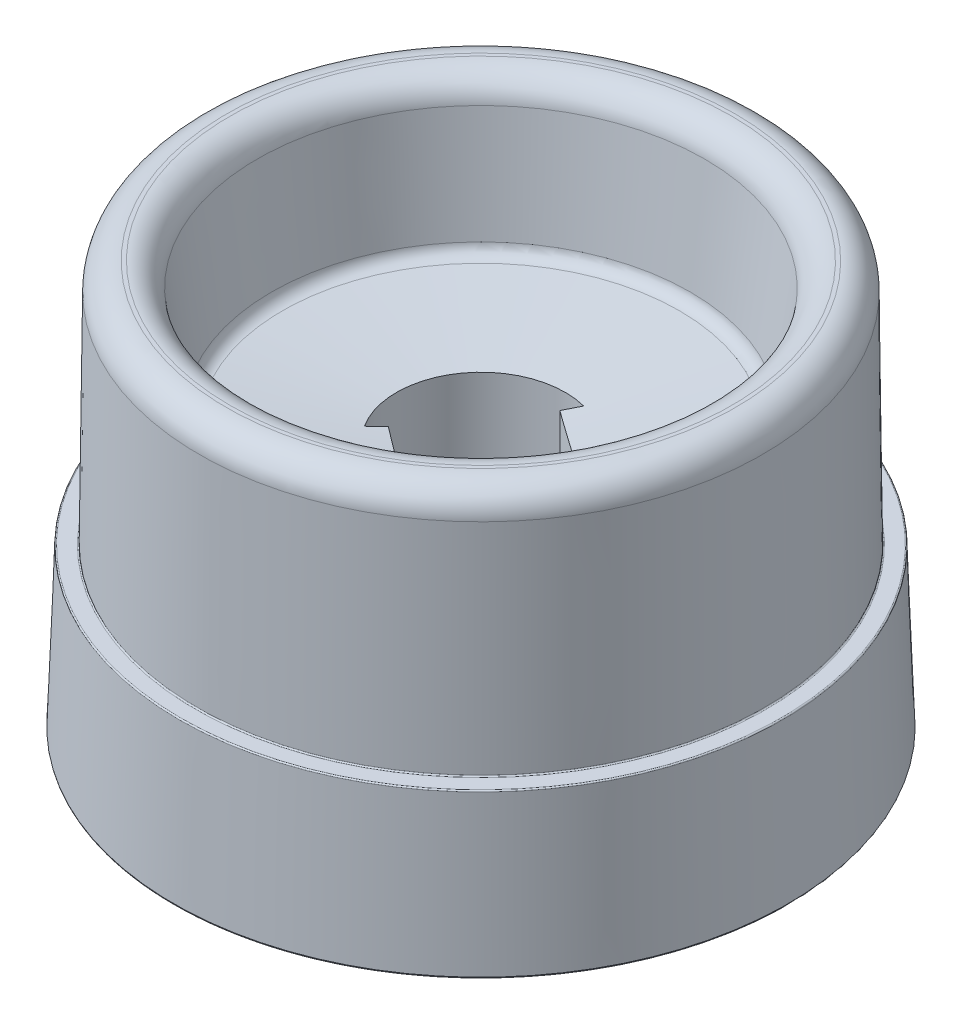
SolidWorks part; units mm, degrees
material "Nikiel"
ref_plane "Płaszczyzna przednia" through (0, 0, 0) normal (0, 0, 1) x (1, 0, 0)
ref_plane "Płaszczyzna górna" through (0, 0, 0) normal (0, 1, 0) x (1, 0, 0)
ref_plane "Płaszczyzna prawa" through (0, 0, 0) normal (1, 0, 0) x (0, 0, -1)
sketch "Szkic1" plane through (0, 0, 0) normal (0, 0, 1) x (1, 0, 0)
  line L0 (9.7791, 0) -> (12.2282, 0)
  line L1 (11.4094, 6.35) -> (12.0018, 6.35)
  line L2 (0, 4.2) -> (9.1594, 4.2)
  line L3 (0, 4.2) -> (0, 9.53)
  line L4 (12.2781, 0.0518) -> (12.0517, 6.3018)
  line L5 (11.3594, 6.3994) -> (11.2621, 15.1022)
  line L6 (10.1721, 16.18) -> (10.025, 16.18)
  line L8 (9.7291, 0.049) -> (9.6593, 3.7095)
  line L9 (8.9445, 15.2333) -> (8.3718, 10.9144)
  line L10 (7.9358, 10.4837) -> (0, 9.53)
  arc A1 (11.2621, 15.1022) -> (10.1721, 16.18) centre (10.1721, 15.09) ccw
  arc A2 (8.9445, 15.2333) -> (10.025, 16.18) centre (10.025, 15.09) cw
  arc A3 (11.3594, 6.3994) -> (11.4094, 6.35) centre (11.4094, 6.4) ccw
  arc A4 (12.0018, 6.35) -> (12.0517, 6.3018) centre (12.0018, 6.3) cw
  arc A5 (9.1594, 4.2) -> (9.6593, 3.7095) centre (9.1594, 3.7) cw
  arc A6 (9.7291, 0.049) -> (9.7791, 0) centre (9.7791, 0.05) ccw
  arc A7 (12.2282, 0) -> (12.2781, 0.0518) centre (12.2282, 0.05) ccw
  arc A8 (8.3718, 10.9144) -> (7.9358, 10.4837) centre (7.8761, 10.9802) cw
  point P13 (11.25, 16.18)
revolve "Obrót3" add sketch "Szkic1" angle 360 about L3
sketch "Szkic2" plane through (0, 4.2, 0) normal (0, -1, 0) x (1, 0, 0)
  line L0 (2.4058, -1.3273) -> (2.7996, -1.8852)
  line L1 (0.4451, -2.7114) -> (2.4058, -1.3273)
  line L2 (0.4451, -2.7114) -> (0.8389, -3.2692)
  line L5 (-2.4377, 1.2678) -> (-2.8451, 1.8158)
  line L6 (-2.4377, 1.2678) -> (-0.5116, 2.6996)
  line L7 (-0.5116, 2.6996) -> (-0.919, 3.2476)
  arc A2 (2.7996, -1.8852) -> (-0.919, 3.2476) centre (0, 0) ccw
  arc A3 (-2.8451, 1.8158) -> (0.8389, -3.2692) centre (0, 0) ccw
extrude "Wytnij-wyciągnięcie1" cut sketch "Szkic2" against normal blind 10
